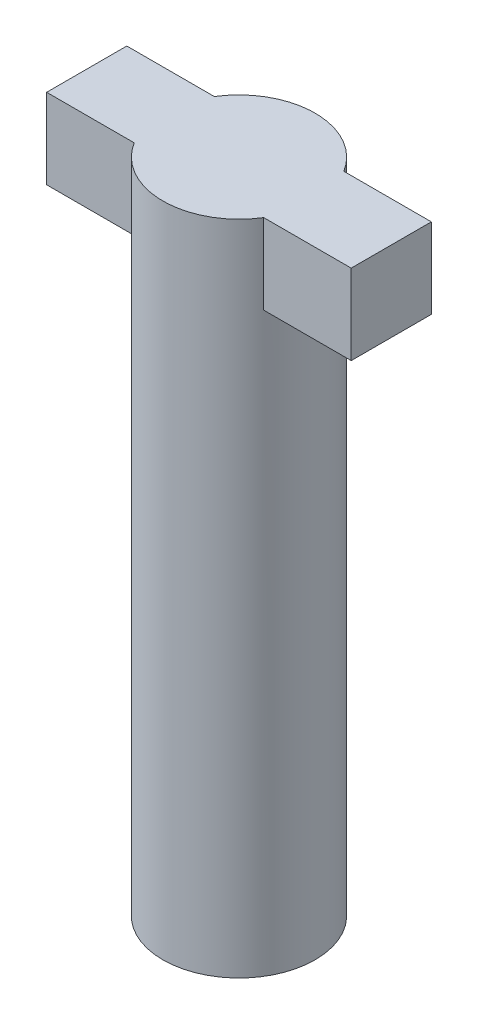
SolidWorks part; units mm, degrees
ref_plane "Front Plane" through (0, 0, 0) normal (0, 0, 1) x (1, 0, 0)
ref_plane "Top Plane" through (0, 0, 0) normal (0, 1, 0) x (1, 0, 0)
ref_plane "Right Plane" through (0, 0, 0) normal (1, 0, 0) x (0, 0, -1)
sketch "Sketch1" plane through (0, 0, 0) normal (0, 1, 0) x (1, 0, 0)
  circle A0 centre (0, 0) radius 0.95
  dimension "D1" = 1.9
extrude "Body" add sketch "Sketch1" along normal blind 8.2
sketch "Sketch2" plane through (0, 8.2, 0) normal (0, 1, 0) x (1, 0, 0)
  line L0 (0, 0) -> (-1.9, 0) construction
  line L1 (0, 0.5) -> (-1.9, 0.5)
  line L2 (0, -0.5) -> (-1.9, -0.5)
  line L3 (-1.9, 0.5) -> (-1.9, -0.5)
  line L4 (0, 0) -> (0, 0.2952) construction
  line L5 (0, 0) -> (1.9, 0) construction
  line L6 (0, -0.5) -> (1.9, -0.5)
  line L7 (1.9, 0.5) -> (1.9, -0.5)
  line L8 (0, 0.5) -> (1.9, 0.5)
  circle A0 centre (0, 0) radius 0.95 construction
  circle A1 centre (0, 0) radius 0.95
  circle M6 centre (0, 0) radius 0.95
  dimension "D1" = 1.9
  dimension "D2" = 0.5
  dimension "D3" = 0.5
extrude "Lock" add sketch "Sketch2" against normal blind 1 contours L1 L3 L2 M6 | L8 L6 L7 M6
equation "\"BoltD\"=2mm"
equation "\"NutShortSide\"=4mm"
equation "\"NutLongSide\"=4.5mm"
equation "\"SmallScrewD\"=1.2mm"
equation "\"SmallScrewHatD\"=2mm"
equation "\"TubeOuterD\"=1.2mm"
equation "\"BasicPulleyD\"=15mm"
equation "\"GrooveDepth\"=0.7mm"
equation "\"Cable1D\"=0.4mm"
equation "\"Cable2D\"=0.3mm"
equation "\"BallBearingInnerD\"=2mm"
equation "\"BallBearingOuterD\"=4mm"
equation "\"D1@Sketch1\"=\"BallBearingInnerD\"-0.1"
equation "\"BoltHatD\"=3.2mm"
equation "\"BallBearingThickness\"=2mm"
equation "\"HumerusL\"=37.2mm"
equation "\"HumerusElbowSidePulleyD\"=10mm"
equation "\"RadiusL\"=68.1mm"
equation "\"Finger1L\"=120mm"
equation "\"Finger2L\"=100mm"
equation "\"Finger3L\"=80mm"
equation "\"ElbowExtendedAngle\"=140deg"
equation "\"ElbowFlexedAngle\"=38deg"
equation "\"BearingCapD\"=12mm"
equation "\"TubeClipW\"=1.5mm"
equation "\"TubeClipH\"=1.5mm"
equation "\"TubeClipLock_SideL\"=1.5mm"
equation "\"TubeClipLock_W\"=0.7mm"
equation "\"Digit5ExtendedAngle\"=80deg"
equation "\"Digit5FlexedAngle\"=24deg"
equation "\"Digit4ExtendedAngle\"=108deg"
equation "\"Digit4FlexedAngle\"=34deg"
equation "\"Digit3ExtendedAngle\"=145deg"
equation "\"Digit3FlexedAngle\"=44deg"
equation "\"XL330_M077_T_FrameBoltD\"=1.6mm"
equation "\"XL330_M077_T_FrameNutShortSide\"=2.5mm"
equation "\"XL330_M077_T_FrameNutLongSide\"=3mm"
equation "\"KST_ServoBoltShelfHeight\"=21.1mm"
equation "\"KST_ServoLength\"=23mm"
equation "\"KST_ServoWidth\"=12mm"
equation "\"KST_ServoBoltHole2HoleLength\"=28mm"
equation "\"KST_ServoBoltHole2ShaftDist\"=8.3mm"
equation "\"KST_ServoBoltHole2HoleWidth\"=7mm"
equation "\"KST_ServoHeight\"=27.5mm"
equation "\"KST_ServoShaftHeight\"=3.5mm"
equation "\"KST_ServoShaftD\"=4.25mm"
equation "\"KST_ServoShaftToothL\"=0.345mm"
equation "\"KST_ServoShaftToothAngle\"=60deg"
equation "\"KST_ServoShaftToothTipWidth\"=0.18mm"
equation "\"KST_ServoShaftToothFilletR\"=0.1mm"
equation "\"KST_ServoShaftToothN\"=25"
equation "\"KST_ServoShaftBoltD\"=2mm"
equation "\"KST_ServoShaftBoltHatD\"=5mm"
equation "\"XL330_M077_T_Length\"=34mm"
equation "\"XL330_M077_T_Width\"=20mm"
equation "\"XL330_M077_T_Height\"=23mm"
equation "\"XL330_M077_T_BoltHole2HoleLength\"=30mm"
equation "\"XL330_M077_T_BoltHole2HoleWidth\"=16mm"
equation "\"XL330_M077_T_BoltHole2ShaftDist\"=7.5mm"
equation "\"XL330_M077_T_HornHeight\"=3mm"
equation "\"XL330_M077_T_HornBoltD\"=2mm"
equation "\"XL330_M077_T_HornBoltHatD\"=5.6mm"
equation "\"XL330_M077_T_HornD\"=16mm"
equation "\"XL330_M077_T_HornScrewHoleCircleD\"=12mm"
equation "\"XL330_M077_T_BoltD\"=1.6mm"
